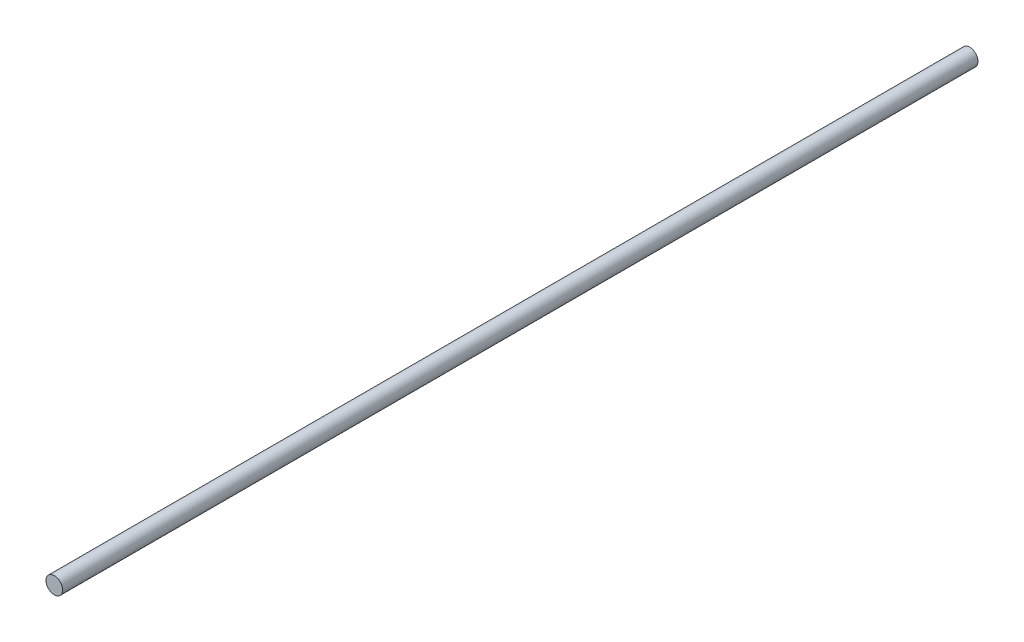
SolidWorks part; units mm, degrees
ref_plane "Front Plane" through (0, 0, 0) normal (0, 0, 1) x (1, 0, 0)
ref_plane "Top Plane" through (0, 0, 0) normal (0, 1, 0) x (1, 0, 0)
ref_plane "Right Plane" through (0, 0, 0) normal (1, 0, 0) x (0, 0, -1)
sketch "Sketch1" plane through (0, 0, 0) normal (0, 0, 1) x (1, 0, 0)
  circle A0 centre (0, 0) radius 10
  dimension "D1" = 20
extrude "Boss-Extrude1" add sketch "Sketch1" along normal blind 1100
